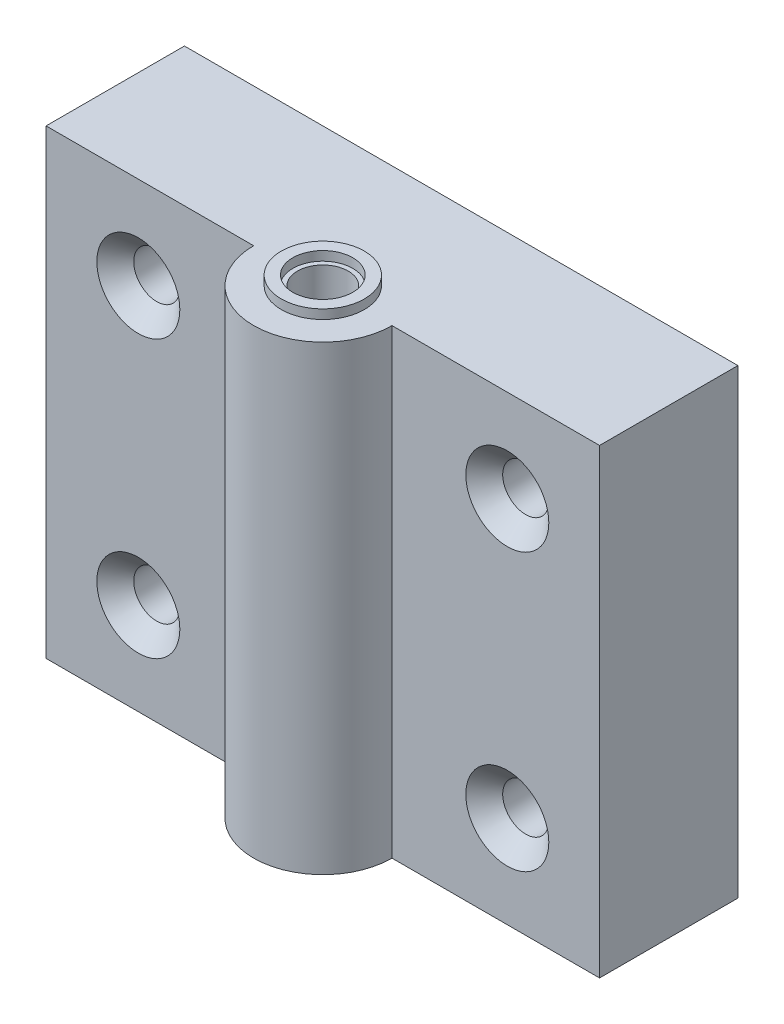
SolidWorks part; units mm, degrees
ref_plane "Plan de face" through (0, 0, 0) normal (0, 0, 1) x (1, 0, 0)
ref_plane "Plan de dessus" through (0, 0, 0) normal (0, 1, 0) x (1, 0, 0)
ref_plane "Plan de droite" through (0, 0, 0) normal (1, 0, 0) x (0, 0, -1)
sketch "Esquisse1" plane through (0, 0, 0) normal (0, 0, 1) x (1, 0, 0)
  line L1 (-30, 25) -> (30, 25)
  line L2 (-30, 25) -> (-30, -25)
  line L3 (-30, -25) -> (30, -25)
  line L4 (30, 25) -> (30, -25)
  line L5 (-30, 25) -> (30, -25) construction
  line L6 (-30, -25) -> (30, 25) construction
  point P0 (0, 0)
  dimension "D1" = 60
  dimension "D2" = 50
extrude "Boss.-Extru.1" add sketch "Esquisse1" along normal blind 15
sketch "Esquisse2" plane through (0, 25, 0) normal (0, 1, 0) x (1, 0, 0)
  line L0 (0, 0) -> (0, -15) construction
  line L1 (30, -15) -> (-30, -15) construction
  line L3 (-7.5, -15) -> (7.5, -15)
  arc A0 (-7.5, -15) -> (7.5, -15) centre (0, -15) ccw
  dimension "D1" = 7.5
extrude "Boss.-Extru.2" add sketch "Esquisse2" against normal blind 50
sketch "Esquisse3" plane through (0, 25, 0) normal (0, 1, 0) x (1, 0, 0)
  line L0 (-7.5, -15) -> (7.5, -15) construction
  circle A0 centre (0, -15) radius 4.5
  circle A1 centre (0, -15) radius 2.75 construction
  circle A2 centre (0, -15) radius 3.25
  dimension "D1" = 9
  dimension "D2" = 5.5
  dimension "D3" = 0.5
extrude "Boss.-Extru.3" add sketch "Esquisse3" along normal blind 1
sketch "Esquisse4" plane through (0, 25, 0) normal (0, 1, 0) x (1, 0, 0)
  circle A0 centre (0, -15) radius 2.75
  dimension "D1" = 5.5
extrude "Enlèv. mat.-Extru.1" cut sketch "Esquisse4" against normal blind 50
sketch "Esquisse5" plane through (0, 0, 15) normal (0, 0, 1) x (1, 0, 0)
  line L0 (-30, 25) -> (-30, -25) construction
  line L3 (-30, -25) -> (-7.5, -25) construction
  line L7 (0, 26) -> (0, -25) construction
  line L8 (3.25, 26) -> (-3.25, 26) construction
  line L9 (-7.5, -25) -> (7.5, -25) construction
  line L10 (-30, 0) -> (30, 0) construction
  line L11 (30, -25) -> (30, 25) construction
  line L14 (-22.5, -15) -> (-17.5, -15) construction
  circle A1 centre (-20, -15) radius 2.5
  circle A2 centre (-20, 15) radius 2.5
  circle A3 centre (20, -15) radius 2.5
  circle A4 centre (20, 15) radius 2.5
  dimension "D1" = 10
  dimension "D2" = 10
  dimension "D3" = 5
extrude "Enlèv. mat.-Extru.2" cut sketch "Esquisse5" against normal blind 15
ref_plane "Plan1" through (0, -15, 0) normal (0, -1, 0) x (1, 0, 0)
sketch "Esquisse12" plane through (0, 0, 15) normal (0, 0, 1) x (1, 0, 0)
  line L0 (-22.5, -15) -> (-24.5, -15) construction
  circle A0 centre (-20, -15) radius 4.5
  circle A1 centre (-20, -15) radius 2.5 construction
  dimension "D1" = 2
sketch "Esquisse13" plane through (0, -15, 0) normal (0, -1, 0) x (1, 0, 0)
  line L0 (-24.5, 15) -> (-22.5, 13)
  line L1 (-22.5, 15) -> (-22.5, 9.8648) construction
  line L2 (-22.5, 15) -> (-24.5, 15) construction
  line L3 (-20, 15) -> (-20, 9.1393) construction
  line L4 (-22.5, 15) -> (-17.5, 15) construction
  line L5 (-24.5, 15) -> (-22.5, 15)
  line L6 (-22.5, 15) -> (-22.5, 13)
  dimension "D1" = 45
revolve "Enlèvement de matière-Révolution1" cut sketch "Esquisse13" angle 360 about L3
pattern_linear "Répétition linéaire1" count 2 spacing 30 along (0, 1, 0) of "Enlèvement de matière-Révolution1"
pattern_linear "Répétition linéaire2" count 2 spacing 40 along (1, 0, 0) of "Répétition linéaire1", "Enlèvement de matière-Révolution1"
